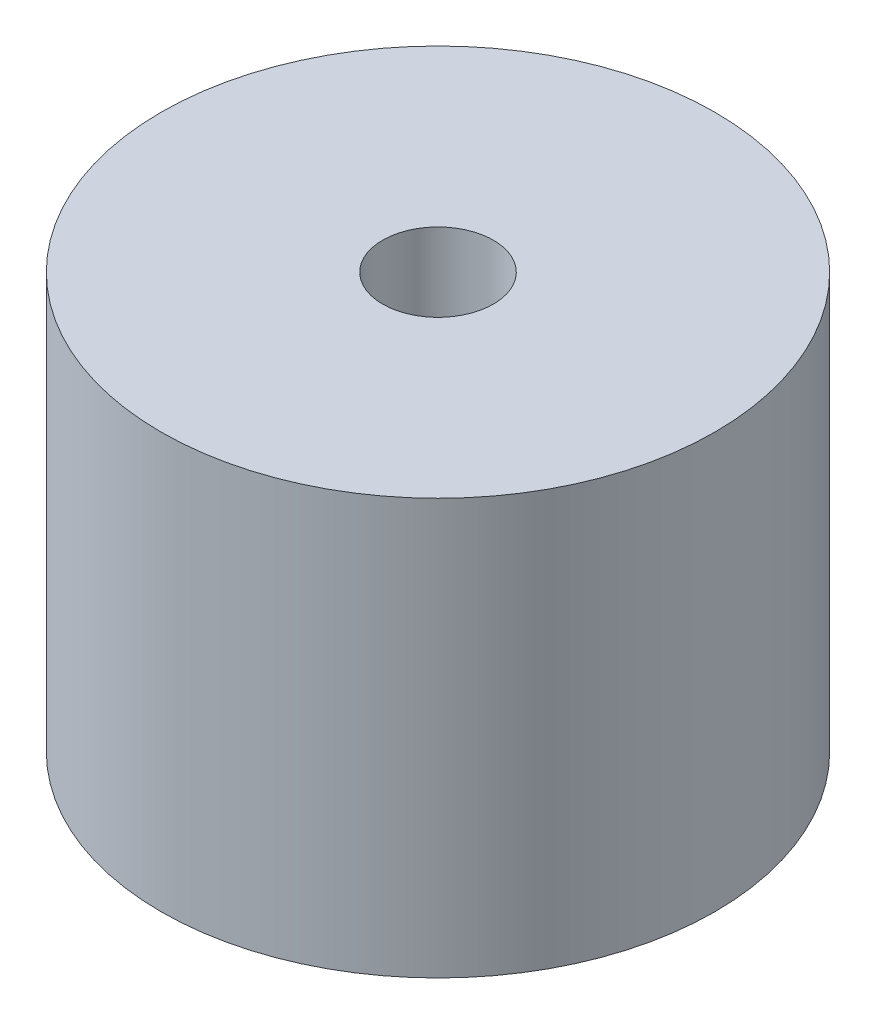
SolidWorks part; units mm, degrees
ref_plane "Front Plane" through (0, 0, 0) normal (0, 0, 1) x (1, 0, 0)
ref_plane "Top Plane" through (0, 0, 0) normal (0, 1, 0) x (1, 0, 0)
ref_plane "Right Plane" through (0, 0, 0) normal (1, 0, 0) x (0, 0, -1)
sketch "Sketch2" plane through (0, 0, 0) normal (0, 1, 0) x (1, 0, 0)
  circle A0 centre (0, 0) radius 10
  circle A1 centre (0, 0) radius 2
extrude "Boss-Extrude1" add sketch "Sketch2" along normal blind 15
